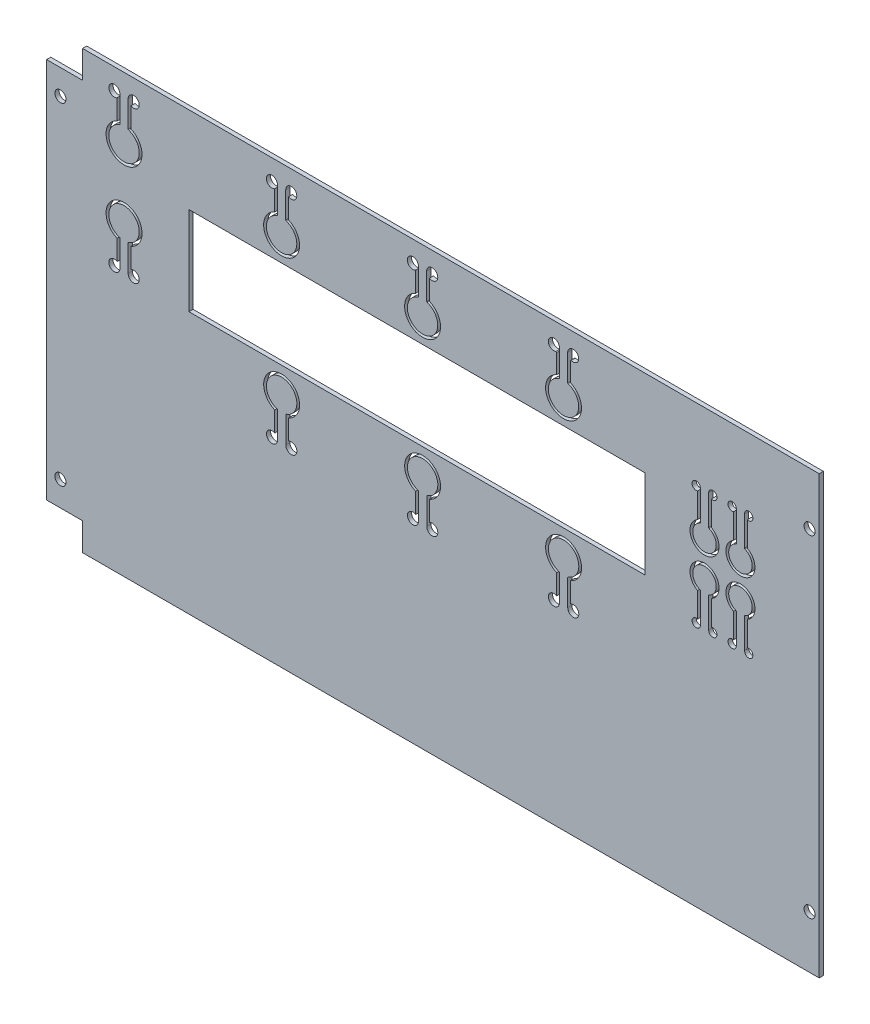
SolidWorks part; units mm, degrees
ref_plane "Plano frontal" through (0, 0, 0) normal (0, 0, 1) x (1, 0, 0)
ref_plane "Plano superior" through (0, 0, 0) normal (0, 1, 0) x (1, 0, 0)
ref_plane "Plano direito" through (0, 0, 0) normal (1, 0, 0) x (0, 0, -1)
sketch "Model" plane through (0, 0, 0) normal (0, 0, 1) x (1, 0, 0)
  line L0 (197.0586, 171.1532) -> (197.0586, 180.8617)
  line L1 (194.0586, 171.1532) -> (194.0586, 180.8617)
  line L2 (194.0586, 180.8617) -> (193.0586, 180.8617)
  line L3 (193.0586, 180.8617) -> (193.0586, 171.8617)
  line L4 (197.0586, 180.8617) -> (198.0586, 180.8617)
  line L5 (198.0586, 180.8617) -> (198.0586, 171.8617)
  line L6 (143.0571, 171.1532) -> (143.0571, 180.8617)
  line L7 (143.0571, 180.8617) -> (142.0571, 180.8617)
  line L8 (142.0571, 180.8617) -> (142.0571, 171.8617)
  line L9 (146.0571, 171.1532) -> (146.0571, 180.8617)
  line L10 (146.0571, 180.8617) -> (147.0571, 180.8617)
  line L11 (147.0571, 180.8617) -> (147.0571, 171.8617)
  line L12 (91.0586, 180.8617) -> (91.0586, 171.8617)
  line L13 (91.0586, 180.8617) -> (92.0586, 180.8617)
  line L14 (92.0586, 180.8617) -> (92.0586, 171.1532)
  line L15 (95.0586, 171.1532) -> (95.0586, 180.8617)
  line L16 (95.0586, 180.8617) -> (96.0586, 180.8617)
  line L17 (96.0586, 180.8617) -> (96.0586, 171.8617)
  line L18 (38.0571, 171.1532) -> (38.0571, 180.8617)
  line L19 (96.0785, 100.8617) -> (96.0785, 109.8617)
  line L20 (95.0785, 100.8617) -> (96.0785, 100.8617)
  line L21 (95.0785, 110.5702) -> (95.0785, 100.8617)
  line L22 (92.0785, 100.8617) -> (92.0785, 110.5702)
  line L23 (91.0785, 100.8617) -> (92.0785, 100.8617)
  line L24 (91.0785, 100.8617) -> (91.0785, 109.8617)
  line L25 (147.0785, 100.8617) -> (147.0785, 109.8617)
  line L26 (146.0785, 100.8617) -> (147.0785, 100.8617)
  line L27 (146.0785, 110.5702) -> (146.0785, 100.8617)
  line L28 (142.0785, 100.8617) -> (142.0785, 109.8617)
  line L29 (143.0785, 100.8617) -> (142.0785, 100.8617)
  line L30 (143.0785, 110.5702) -> (143.0785, 100.8617)
  line L31 (198.08, 100.8617) -> (198.08, 109.8617)
  line L32 (197.08, 100.8617) -> (198.08, 100.8617)
  line L33 (193.08, 100.8617) -> (193.08, 109.8617)
  line L34 (194.08, 100.8617) -> (193.08, 100.8617)
  line L35 (194.08, 110.5702) -> (194.08, 100.8617)
  line L36 (197.08, 110.5702) -> (197.08, 100.8617)
  line L37 (38.0571, 180.8617) -> (39.0571, 180.8617)
  line L38 (39.0571, 180.8617) -> (39.0571, 171.8617)
  line L39 (35.0571, 171.1532) -> (35.0571, 180.8617)
  line L40 (35.0571, 180.8617) -> (34.0571, 180.8617)
  line L41 (34.0571, 180.8617) -> (34.0571, 171.8617)
  line L42 (23.9176, 153.4867) -> (65.6576, 153.4867)
  line L43 (34.0571, 126.1117) -> (34.0571, 135.1117)
  line L44 (35.0571, 126.1117) -> (34.0571, 126.1117)
  line L45 (35.0571, 135.8202) -> (35.0571, 126.1117)
  line L46 (39.0571, 126.1117) -> (39.0571, 135.1117)
  line L47 (38.0571, 126.1117) -> (39.0571, 126.1117)
  line L48 (38.0571, 135.8202) -> (38.0571, 126.1117)
  line L49 (248.0586, 151.3382) -> (248.0586, 162.3617)
  line L50 (248.0586, 162.3617) -> (249.0586, 162.3617)
  line L51 (249.0586, 162.3617) -> (249.0586, 151.9782)
  line L52 (245.0586, 151.3382) -> (245.0586, 162.3617)
  line L53 (245.0586, 162.3617) -> (244.0586, 162.3617)
  line L54 (244.0586, 162.3617) -> (244.0586, 151.9782)
  line L55 (225.0586, 140.8617) -> (284.5378, 140.8617)
  line L56 (258.0913, 130.373) -> (258.0913, 119.3617)
  line L57 (262.0586, 162.2728) -> (262.0586, 151.9782)
  line L58 (261.0259, 162.2728) -> (262.0586, 162.2728)
  line L59 (261.0259, 151.3503) -> (261.0259, 162.2728)
  line L60 (257.0586, 162.3617) -> (257.0586, 151.9782)
  line L61 (258.0913, 162.3617) -> (257.0586, 162.3617)
  line L62 (258.0913, 151.3503) -> (258.0913, 162.3617)
  line L63 (258.0913, 119.3617) -> (257.0586, 119.3617)
  line L64 (257.0586, 119.3617) -> (257.0586, 129.7451)
  line L65 (261.0259, 130.373) -> (261.0259, 119.4505)
  line L66 (261.0259, 119.4505) -> (262.0586, 119.4505)
  line L67 (262.0586, 119.4505) -> (262.0586, 129.7451)
  line L68 (244.0586, 119.3617) -> (244.0586, 129.7451)
  line L69 (245.0586, 119.3617) -> (244.0586, 119.3617)
  line L70 (245.0586, 130.3852) -> (245.0586, 119.3617)
  line L71 (249.0586, 119.3617) -> (249.0586, 129.7451)
  line L72 (248.0586, 119.3617) -> (249.0586, 119.3617)
  line L73 (248.0586, 130.3852) -> (248.0586, 119.3617)
  line L96 (225.0586, 125.1117) -> (225.0586, 157.1117)
  line L97 (225.0586, 157.1117) -> (60.0586, 157.1117)
  line L98 (60.0586, 157.1117) -> (60.0586, 125.1117)
  line L99 (60.0586, 125.1117) -> (225.0586, 125.1117)
  line L102 (22.0586, 22.3617) -> (288.0586, 22.3617)
  line L103 (22.0461, 30.3617) -> (22.0586, 22.3617)
  line L104 (12.0461, 30.3617) -> (22.0461, 30.3617)
  line L105 (12.0586, 40.3617) -> (12.0461, 30.3617)
  line L106 (4.0586, 40.3617) -> (12.0586, 40.3617)
  line L107 (4.0586, 178.3617) -> (4.0586, 40.3617)
  line L108 (12.0586, 178.3617) -> (4.0586, 178.3617)
  line L109 (12.0586, 188.3617) -> (12.0586, 178.3617)
  line L110 (22.0586, 188.3617) -> (12.0586, 188.3617)
  line L111 (22.0586, 196.3617) -> (22.0586, 188.3617)
  line L112 (288.0586, 196.3617) -> (22.0586, 196.3617)
  line L117 (288.0586, 22.3617) -> (288.0586, 196.3617)
  arc A0 (34.0571, 171.8617) -> (39.0571, 171.8617) centre (36.5571, 165.8617) ccw
  arc A1 (39.0571, 135.1046) -> (36.5657, 147.6117) centre (36.5742, 141.1117) ccw
  circle A2 centre (90.0785, 100.8617) radius 2
  circle A3 centre (97.0785, 100.8617) radius 2
  circle A4 centre (141.0785, 100.8617) radius 2
  arc A5 (193.0586, 171.8617) -> (198.0586, 171.8617) centre (195.5586, 165.8617) ccw
  arc A6 (142.0571, 171.8617) -> (147.0571, 171.8617) centre (144.5571, 165.8617) ccw
  arc A7 (91.0586, 171.8617) -> (96.0586, 171.8617) centre (93.5586, 165.8617) ccw
  arc A8 (244.0586, 151.9782) -> (249.0586, 151.9782) centre (246.5586, 147.3617) ccw
  arc A9 (257.0586, 151.9782) -> (262.0586, 151.9782) centre (259.5586, 147.3617) ccw
  arc A10 (262.0586, 129.7451) -> (257.0586, 129.7451) centre (259.5586, 134.3617) ccw
  arc A11 (249.0586, 129.7451) -> (244.0586, 129.7451) centre (246.5586, 134.3617) ccw
  arc A12 (194.0586, 171.1532) -> (197.0586, 171.1532) centre (195.5586, 165.8617) ccw
  arc A13 (143.0571, 171.1532) -> (146.0571, 171.1532) centre (144.5571, 165.8617) ccw
  arc A14 (92.0586, 171.1532) -> (95.0586, 171.1532) centre (93.5586, 165.8617) ccw
  circle A15 centre (199.0586, 180.8617) radius 2
  circle A16 centre (192.0586, 180.8617) radius 2
  circle A17 centre (148.0571, 180.8617) radius 2
  circle A18 centre (141.0571, 180.8617) radius 2
  circle A19 centre (97.0571, 180.8617) radius 1.9985
  circle A20 centre (90.0586, 180.8617) radius 2
  circle A21 centre (148.0785, 100.8617) radius 2
  circle A22 centre (192.08, 100.8617) radius 2
  circle A23 centre (199.08, 100.8617) radius 2
  arc A24 (92.0785, 110.5702) -> (95.0785, 110.5702) centre (93.5785, 115.8617) cw
  arc A25 (143.0785, 110.5702) -> (146.0785, 110.5702) centre (144.5785, 115.8617) cw
  arc A26 (194.08, 110.5702) -> (197.08, 110.5702) centre (195.58, 115.8617) cw
  arc A27 (91.0785, 109.8617) -> (96.0785, 109.8617) centre (93.5785, 115.8617) cw
  arc A28 (142.0785, 109.8617) -> (147.0785, 109.8617) centre (144.5785, 115.8617) cw
  arc A29 (193.08, 109.8617) -> (198.08, 109.8617) centre (195.58, 115.8617) cw
  arc A30 (35.0571, 171.1532) -> (38.0571, 171.1532) centre (36.5571, 165.8617) ccw
  circle A31 centre (40.0571, 180.8617) radius 2
  circle A32 centre (33.0571, 180.8617) radius 2
  circle A33 centre (33.0571, 126.1117) radius 2
  circle A34 centre (40.0571, 126.1117) radius 2
  arc A35 (35.0571, 135.8202) -> (38.0571, 135.8202) centre (36.5571, 141.1117) cw
  arc A36 (34.0571, 135.1117) -> (39.0571, 135.1117) centre (36.5571, 141.1117) cw
  arc A37 (245.0586, 151.3382) -> (248.0586, 151.3382) centre (246.5586, 147.3617) ccw
  circle A38 centre (249.5586, 162.3617) radius 1.5
  circle A39 centre (243.5586, 162.3617) radius 1.5
  circle A40 centre (262.5586, 162.3617) radius 1.5
  circle A41 centre (256.5586, 162.3617) radius 1.5
  arc A42 (261.0259, 151.3503) -> (258.0913, 151.3503) centre (259.5586, 147.3617) cw
  arc A43 (262.0586, 151.9782) -> (257.0586, 151.9782) centre (259.5586, 147.3617) cw
  arc A44 (262.0586, 129.7451) -> (257.0586, 129.7451) centre (259.5586, 134.3617) ccw
  arc A45 (261.0259, 130.373) -> (258.0913, 130.373) centre (259.5586, 134.3617) ccw
  circle A46 centre (256.5586, 119.3617) radius 1.5
  circle A47 centre (262.5586, 119.3617) radius 1.5
  circle A48 centre (243.5586, 119.3617) radius 1.5
  circle A49 centre (249.5586, 119.3617) radius 1.5
  arc A50 (245.0586, 130.3852) -> (248.0586, 130.3852) centre (246.5586, 134.3617) cw
  arc A51 (257.0586, 129.7451) -> (262.0586, 129.7451) centre (259.5586, 134.3617) cw
  arc A52 (244.0586, 129.7451) -> (249.0586, 129.7451) centre (246.5586, 134.3617) cw
  dimension "D11" = 10.5
  dimension "D12" = 6.5
  dimension "D13" = 10.5
  dimension "D14" = 9.25
  dimension "D15" = 13
  dimension "D16" = 1.5
  dimension "D18" = 5.5
  dimension "D26" = 11
  dimension "D27" = 15
  dimension "D28" = 6.5
  dimension "D30" = 9.75
  dimension "D31" = 29.5
  dimension "D32" = 13
  dimension "D33" = 11
  dimension "D40" = 9.25
  dimension "D41" = 21.5
  dimension "D46" = 13
  dimension "D47" = 11
  dimension "D50" = 3
  dimension "D51" = 1.5
  dimension "D52" = 15
  dimension "D53" = 8.75
  dimension "D29" = 1
  dimension "D54" = 33.5
  dimension "D55" = 12.375
  dimension "D56" = 24.75
  dimension "D57" = 1
  dimension "D62" = 15
  dimension "D63" = 15
  dimension "D64" = 15
  dimension "D65" = 15
  dimension "D66" = 15
  dimension "D67" = 15
  dimension "D1" = 284
  dimension "D2" = 174
  dimension "D3" = 10
  dimension "D4" = 8
  dimension "D5" = 10
  dimension "D6" = 8
  dimension "D7" = 8
  dimension "D8" = 10
  dimension "D9" = 8
  dimension "D10" = 10
  dimension "D17" = 3
  dimension "D19" = 1
  dimension "D20" = 39.25
  dimension "D21" = 32
  dimension "D22" = 165
  dimension "D23" = 56
  dimension "D24" = 1
  dimension "D25" = 1
  dimension "D34" = 3
  dimension "D35" = 1.5
  dimension "D36" = 1
  dimension "D37" = 1
  dimension "D38" = 15
  dimension "D39" = 15
  dimension "D42" = 3
  dimension "D43" = 1.5
  dimension "D44" = 1
  dimension "D45" = 1
  dimension "D48" = 15
  dimension "D49" = 15
  dimension "D58" = 1
  dimension "D59" = 3
  dimension "D60" = 1.5
  dimension "D61" = 15
extrude "Ressalto-extrusão1" add sketch "Model" along normal blind 1.5
sketch "Esboço1" plane through (0, 0, 0) normal (0, 0, -1) x (-1, 0, 0)
  line L0 (-288.0742, 188.3617) -> (-21.5586, 188.3617)
  line L1 (-288.0742, 196.3617) -> (-288.0742, 188.3617)
  line L2 (-288.0742, 30.3617) -> (-288.0742, 22.3617)
  line L3 (-22.0586, 22.3617) -> (-288.0586, 22.3617) construction
  line L9 (-288.0742, 30.3617) -> (-21.5586, 30.3617)
  line L19 (-288.0742, 196.3617) -> (-4.0586, 196.3617)
  line L21 (-288.0586, 196.3617) -> (-22.0586, 196.3617) construction
  line L22 (-4.0586, 22.3617) -> (-288.0742, 22.3617)
  line L23 (-4.0586, 196.3617) -> (-4.0586, 22.3617)
  line L27 (-8.5586, 178.3617) -> (-8.5586, 40.3617)
  line L28 (-4.0586, 178.3617) -> (-4.0586, 40.3617) construction
  line L33 (-21.5586, 30.3617) -> (-21.5586, 40.3617)
  line L34 (-21.5586, 40.3617) -> (-8.5586, 40.3617)
  line L35 (-21.5586, 188.3617) -> (-21.5586, 178.3617)
  line L36 (-21.5586, 178.3617) -> (-8.5586, 178.3617)
  dimension "D5" = 10
  dimension "D1" = 8
  dimension "D2" = 8
  dimension "D4" = 4.5
  dimension "D6" = 13
  dimension "D7" = 13
  dimension "D8" = 10
extrude "Corte-extrusão1" cut sketch "Esboço1" against normal blind 10
sketch "Esboço2" plane through (0, 0, 1.5) normal (0, 0, 1) x (1, 0, 0)
  line L0 (288.0586, 30.3617) -> (288.0586, 188.3617) construction
  line L1 (8.5586, 178.3617) -> (8.5586, 40.3617) construction
  line L3 (288.0586, 30.3617) -> (22.0461, 30.3617) construction
  line L5 (21.5586, 30.3617) -> (22.0461, 30.3617) construction
  circle A0 centre (284.5586, 169.3617) radius 2
  circle A1 centre (284.5586, 49.3617) radius 2
  circle A2 centre (13.5586, 49.3618) radius 2
  circle A3 centre (13.5586, 169.3618) radius 2
  dimension "D1" = 3.5
  dimension "D2" = 3.5
  dimension "D3" = 5
  dimension "D4" = 5
  dimension "D5" = 120
  dimension "D6" = 120
  dimension "D7" = 19
  dimension "D8" = 19
extrude "Corte-extrusão2" cut sketch "Esboço2" against normal through all
fillet "Filete1" radius 0.25 26 edges at (193.0586, 179.1296, 0.75) (198.0586, 179.1296, 0.75) (197.0586, 171.1532, 0.75) (194.0586, 171.1532, 0.75) (258.0913, 130.373, 0.75) (245.0586, 130.3852, 0.75) (258.0913, 151.3503, 0.75) (245.0586, 151.3382, 0.75) (248.0586, 130.3852, 0.75) (261.0259, 130.373, 0.75) (261.0259, 151.3503, 0.75) (248.0586, 151.3382, 0.75) (38.0571, 171.1532, 0.75) (38.0571, 135.8202, 0.75) (95.0785, 110.5702, 0.75) (146.0785, 110.5702, 0.75) (197.08, 110.5702, 0.75) (194.08, 110.5702, 0.75) (143.0785, 110.5702, 0.75) (92.0785, 110.5702, 0.75) (35.0571, 135.8202, 0.75) (35.0571, 171.1532, 0.75) (92.0586, 171.1532, 0.75) (95.0586, 171.1532, 0.75) (146.0571, 171.1532, 0.75) (143.0571, 171.1532, 0.75)
